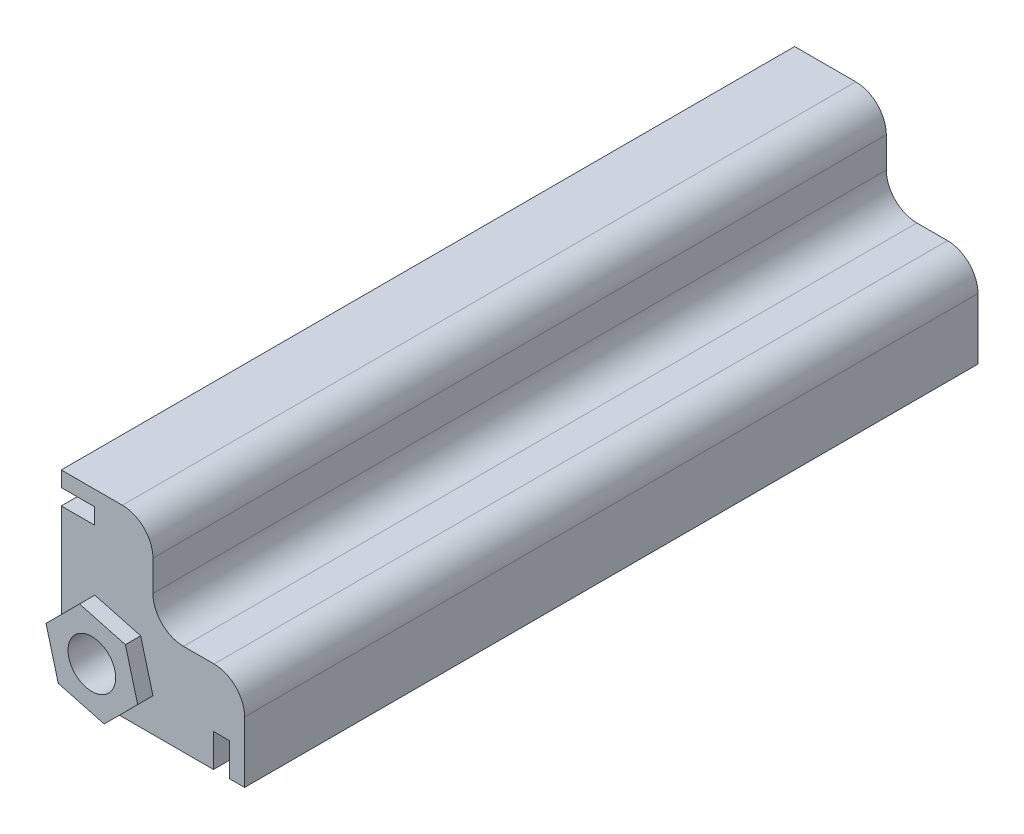
SolidWorks part; units mm, degrees
ref_plane "Front Plane" through (0, 0, 0) normal (0, 0, 1) x (1, 0, 0)
ref_plane "Top Plane" through (0, 0, 0) normal (0, 1, 0) x (1, 0, 0)
ref_plane "Right Plane" through (0, 0, 0) normal (1, 0, 0) x (0, 0, -1)
sketch "Sketch1" plane through (0, 0, 0) normal (0, 0, 1) x (1, 0, 0)
  line L0 (0, 0) -> (0, 38.1)
  line L1 (0, 38.1) -> (19.05, 38.1)
  line L2 (19.05, 38.1) -> (19.05, 19.05)
  line L3 (19.05, 19.05) -> (38.1, 19.05)
  line L4 (38.1, 19.05) -> (38.1, 0)
  line L5 (38.1, 0) -> (0, 0)
  dimension "D1" = 38.1
  dimension "D2" = 38.1
  dimension "D3" = 19.05
  dimension "D4" = 19.05
extrude "Boss-Extrude1" add sketch "Sketch1" along normal blind 152.4
sketch "Sketch2" plane through (0, 0, 152.4) normal (0, 0, 1) x (1, 0, 0)
  line L12 (0, 38.1) -> (0, 0) construction
  line L13 (0, 34.925) -> (6.858, 34.925)
  line L14 (0, 34.925) -> (0, 31.623)
  line L15 (0, 31.623) -> (6.858, 31.623)
  line L16 (6.858, 34.925) -> (6.858, 31.623)
  line L17 (0, 0) -> (38.1, 0) construction
  line L18 (34.925, 0) -> (31.623, 0)
  line L19 (34.925, 0) -> (34.925, 6.858)
  line L20 (34.925, 6.858) -> (31.623, 6.858)
  line L21 (31.623, 0) -> (31.623, 6.858)
  line L22 (19.05, 38.1) -> (0, 38.1) construction
  line L23 (38.1, 0) -> (38.1, 19.05) construction
  dimension "D1" = 3.175
  dimension "D2" = 3.302
  dimension "D3" = 6.858
  dimension "D4" = 3.175
  dimension "D5" = 3.302
  dimension "D6" = 6.858
extrude "Cut-Extrude1" cut sketch "Sketch2" against normal through all
sketch "Sketch3" plane through (0, 0, 152.4) normal (0, 0, 1) x (1, 0, 0)
  line L0 (19.05, 38.1) -> (0, 38.1) construction
  line L5 (16.4978, 16.4978) -> (6.9728, 19.05)
  line L6 (6.9728, 19.05) -> (0, 12.0772)
  line L7 (0, 12.0772) -> (2.5522, 2.5522)
  line L8 (2.5522, 2.5522) -> (12.0772, 0)
  line L9 (12.0772, 0) -> (19.05, 6.9728)
  line L10 (19.05, 6.9728) -> (16.4978, 16.4978)
  line L11 (38.1, 0) -> (38.1, 19.05) construction
  line L12 (9.525, 9.525) -> (19.05, 19.05) construction
  line L13 (0, 0) -> (31.623, 0) construction
  circle A0 centre (9.525, 9.525) radius 8.5399 construction
  point P13 (9.525, 38.1)
  point P16 (38.1, 9.525)
  dimension "D1" = 17.0798
  dimension "D2" = 28.575
extrude "Boss-Extrude2" add sketch "Sketch3" along normal blind 3.175
fillet "Fillet1" radius 6.35 3 edges at (19.05, 19.05, 76.2) (38.1, 19.05, 76.2) (19.05, 38.1, 76.2)
sketch "Sketch4" plane through (0, 0, 155.575) normal (0, 0, 1) x (1, 0, 0)
  line L0 (0, 0) -> (12.0772, 0) construction
  line L5 (0, 12.0772) -> (0, 0) construction
  circle A0 centre (9.525, 9.525) radius 4.953
  dimension "D3" = 9.906
  dimension "D1" = 9.525
  dimension "D2" = 9.525
extrude "Cut-Extrude2" cut sketch "Sketch4" against normal through all
